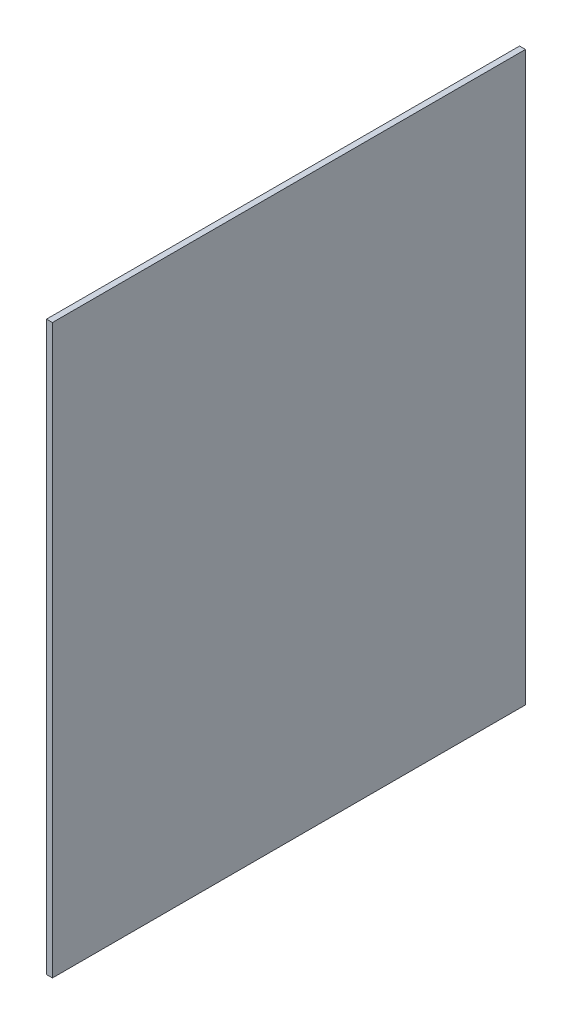
SolidWorks part; units mm, degrees
ref_plane "Front Plane" through (0, 0, 0) normal (0, 0, 1) x (1, 0, 0)
ref_plane "Top Plane" through (0, 0, 0) normal (0, 1, 0) x (1, 0, 0)
ref_plane "Right Plane" through (0, 0, 0) normal (1, 0, 0) x (0, 0, -1)
sketch "Sketch1" plane through (0, 0, 0) normal (1, 0, 0) x (0, 0, -1)
  line L1 (0, 0) -> (508, 0)
  line L2 (0, 0) -> (0, -609.6)
  line L3 (0, -609.6) -> (508, -609.6)
  line L4 (508, 0) -> (508, -609.6)
  point P4 (0, 0)
  dimension "D1" = 609.6
  dimension "D2" = 508
extrude "Boss-Extrude1" add sketch "Sketch1" along normal blind 6.35
